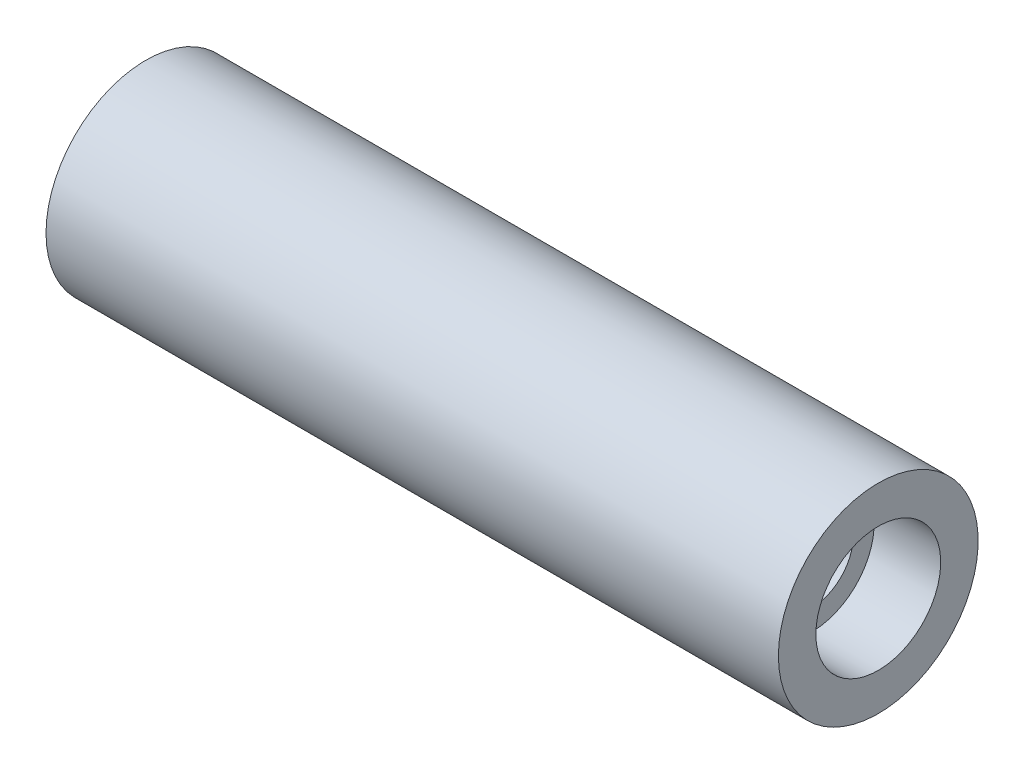
SolidWorks part; units mm, degrees
ref_plane "Front Plane" through (0, 0, 0) normal (0, 0, 1) x (1, 0, 0)
ref_plane "Top Plane" through (0, 0, 0) normal (0, 1, 0) x (1, 0, 0)
ref_plane "Right Plane" through (0, 0, 0) normal (1, 0, 0) x (0, 0, -1)
sketch "Sketch1" plane through (0, 0, 0) normal (0, 0, 1) x (1, 0, 0)
  line L0 (236.9842, 0) -> (285.0657, 0) construction
  line L1 (0, 3.175) -> (50.8, 3.175)
  line L2 (50.8, 3.175) -> (50.8, 4.7625)
  line L3 (50.8, 4.7625) -> (55.88, 4.7625)
  line L4 (55.88, 4.7625) -> (55.88, 7.62)
  line L5 (55.88, 7.62) -> (0, 7.62)
  line L6 (0, 7.62) -> (0, 3.175)
  dimension "D1" = 6.35
  dimension "D2" = 15.24
  dimension "D3" = 55.88
  dimension "D4" = 50.8
  dimension "D5" = 9.525
revolve "Revolve1" add sketch "Sketch1" angle 360 about L0
